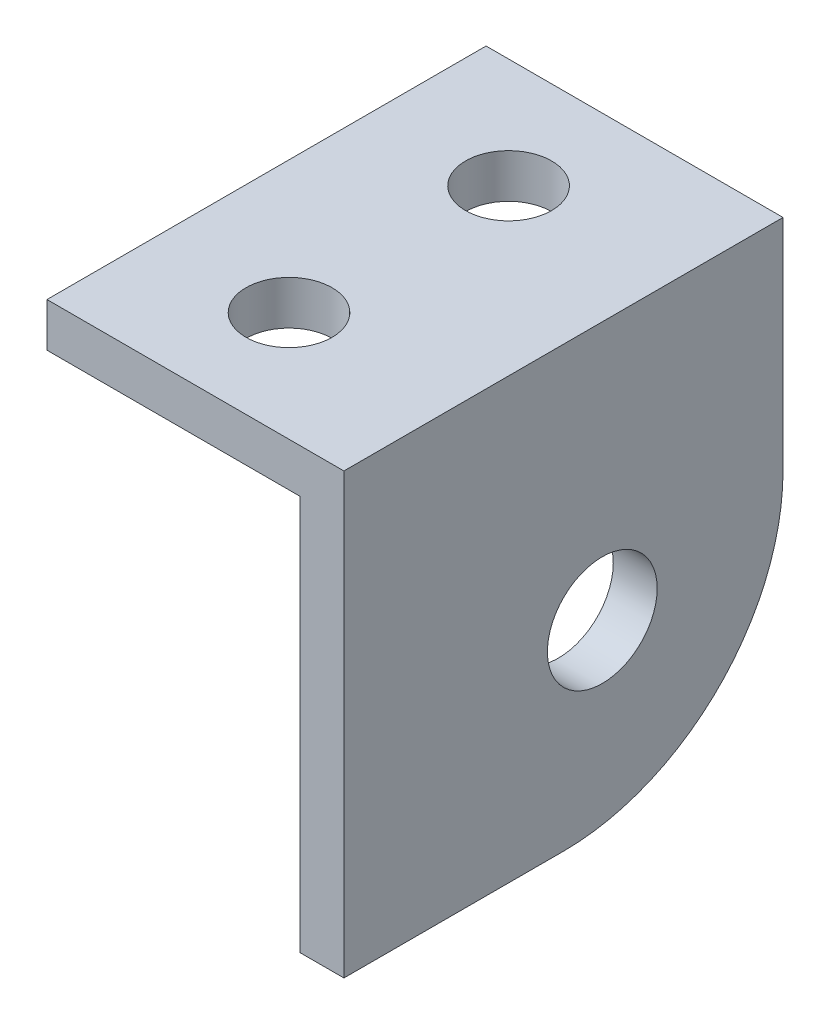
SolidWorks part; units mm, degrees
ref_plane "Front Plane" through (0, 0, 0) normal (0, 0, 1) x (1, 0, 0)
ref_plane "Top Plane" through (0, 0, 0) normal (0, 1, 0) x (1, 0, 0)
ref_plane "Right Plane" through (0, 0, 0) normal (1, 0, 0) x (0, 0, -1)
sketch "Sketch1" plane through (0, 0, 0) normal (0, 0, 1) x (1, 0, 0)
  line L4 (-10.16, -12.7) -> (-10.16, 12.7)
  line L8 (-12.7, 10.16) -> (-12.7, -12.7)
  line L9 (-12.7, -12.7) -> (-10.16, -12.7)
  line L10 (-27.3367, 10.16) -> (-27.3367, 12.7)
  line L11 (-27.3367, 12.7) -> (-10.16, 12.7)
  line L12 (-27.3367, 10.16) -> (-12.7, 10.16)
  point P0 (0, 0)
  point P6 (-11.43, -12.7)
  dimension "D1" = 22.86
  dimension "D2" = 2.54
  dimension "D3" = 25.4
  dimension "D4" = 17.1768
  dimension "D5" = 2.54
  dimension "D6" = 12.7
extrude "Boss-Extrude1" add sketch "Sketch1" along normal blind 25.4
fillet "Fillet1" radius 12.7 1 edges at (-11.43, -12.7, 0)
sketch "Sketch2" plane through (-10.16, 0, 0) normal (1, 0, 0) x (0, 0, -1)
  line L0 (0, 10.16) -> (0, 0) construction
  line L1 (-12.7, 0) -> (-3.7197, -8.9803) construction
  circle A0 centre (-12.7, 0) radius 12.7 construction
  circle A1 centre (-10.4549, -2.2451) radius 3.175
  dimension "D1" = 6.35
  dimension "D3" = 10.4549
  dimension "D2" = 3.175
extrude "Cut-Extrude1" cut sketch "Sketch2" against normal through all
sketch "Sketch3" plane through (-0.012, 10.16, 0) normal (0, -1, 0) x (1, 0, 0)
  line L4 (-10.148, 25.4) -> (-10.148, 12.7) construction
  circle A0 centre (-19.673, 19.05) radius 2.4892
  circle A1 centre (-19.673, 6.35) radius 2.4892
  dimension "D1" = 4.9784
  dimension "D6" = 4.9784
  dimension "D4" = 9.525
extrude "Cut-Extrude2" cut sketch "Sketch3" against normal through all
equation "\"D6@Sketch3\"=\"D1@Sketch3\""
